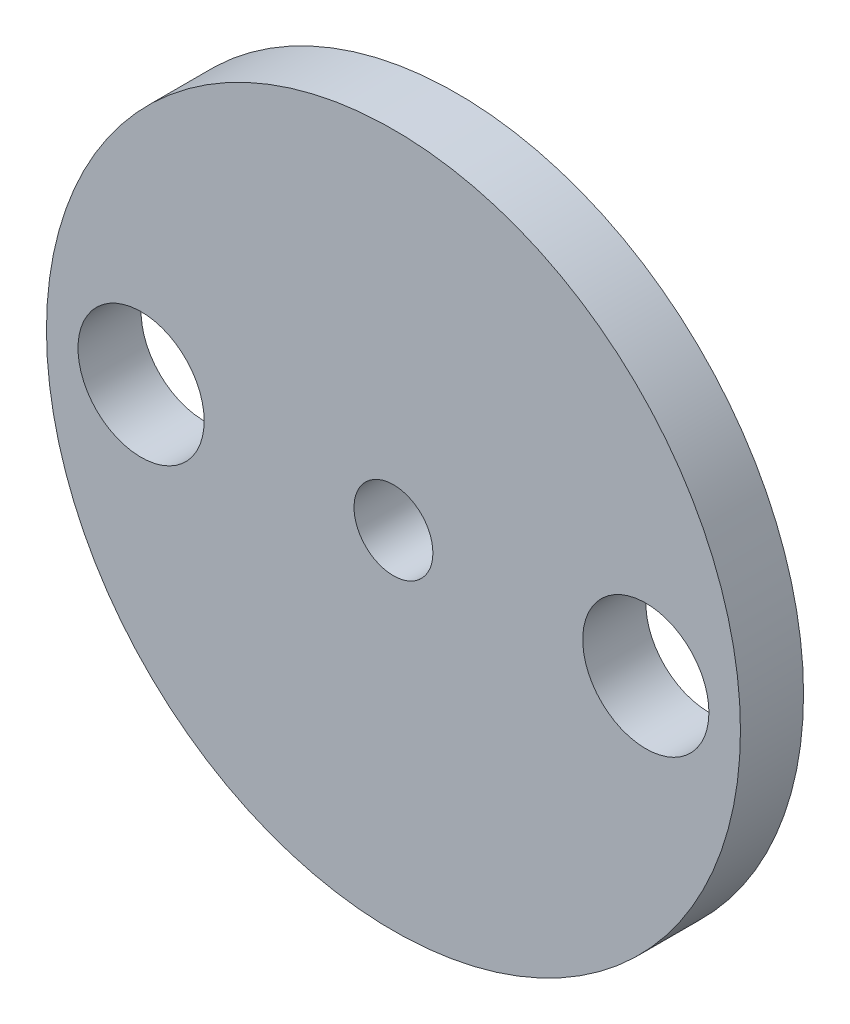
SolidWorks part; units mm, degrees
material "Acrylic (Medium-high impact)"
ref_plane "Front Plane" through (0, 0, 0) normal (0, 0, 1) x (1, 0, 0)
ref_plane "Top Plane" through (0, 0, 0) normal (0, 1, 0) x (1, 0, 0)
ref_plane "Right Plane" through (0, 0, 0) normal (1, 0, 0) x (0, 0, -1)
sketch "Model" plane through (0, 0, 0) normal (0, 0, 1) x (1, 0, 0)
  circle A311 centre (0, 0) radius 11
  circle A312 centre (8, 0) radius 2
  circle A313 centre (-8, 0) radius 2
  circle A314 centre (0, 0) radius 1.25
  dimension "D1" = 4
  dimension "D2" = 2.5
  dimension "D3" = 22
  dimension "D4" = 8
  dimension "D5" = 8
extrude "Boss-Extrude1" add sketch "Model" along normal blind 2
